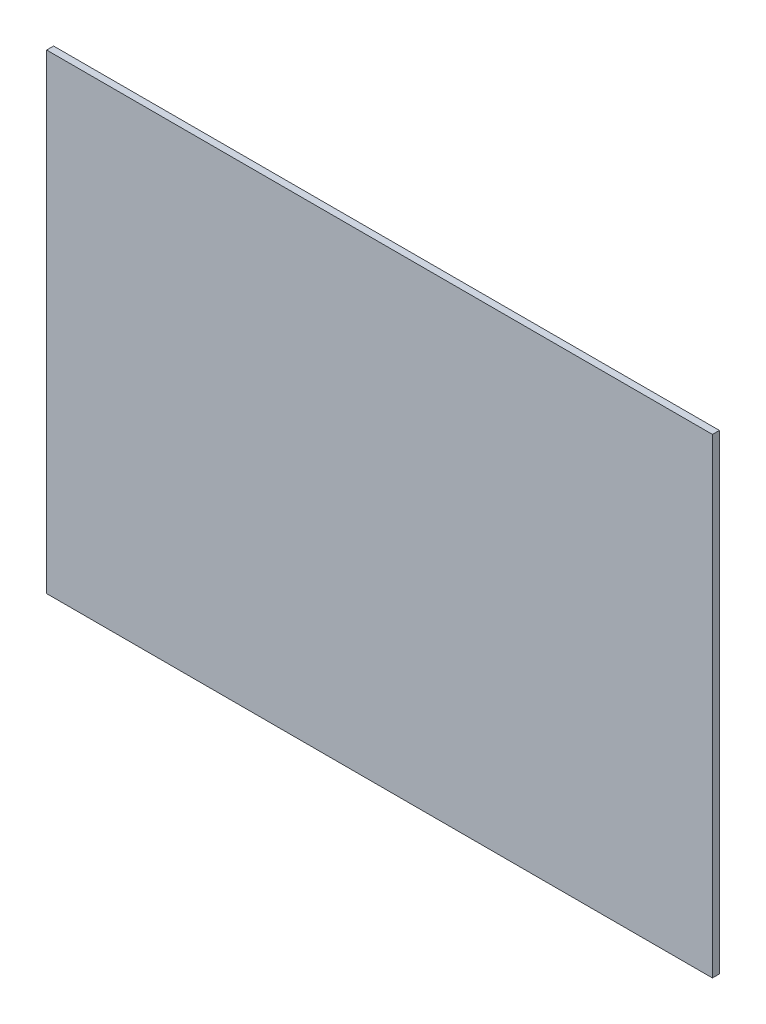
SolidWorks part; units mm, degrees
ref_plane "Front Plane" through (0, 0, 0) normal (0, 0, 1) x (1, 0, 0)
ref_plane "Top Plane" through (0, 0, 0) normal (0, 1, 0) x (1, 0, 0)
ref_plane "Right Plane" through (0, 0, 0) normal (1, 0, 0) x (0, 0, -1)
sketch "Sketch1" plane through (0, 0, 0) normal (0, 0, 1) x (1, 0, 0)
  line L1 (-148.5, -105) -> (148.5, -105)
  line L2 (-148.5, -105) -> (-148.5, 105)
  line L3 (-148.5, 105) -> (148.5, 105)
  line L4 (148.5, -105) -> (148.5, 105)
  line L5 (-148.5, -105) -> (148.5, 105) construction
  line L6 (-148.5, 105) -> (148.5, -105) construction
  point P0 (0, 0)
  dimension "D1" = 297
  dimension "D2" = 210
extrude "Boss-Extrude1" add sketch "Sketch1" along normal blind 3.1
